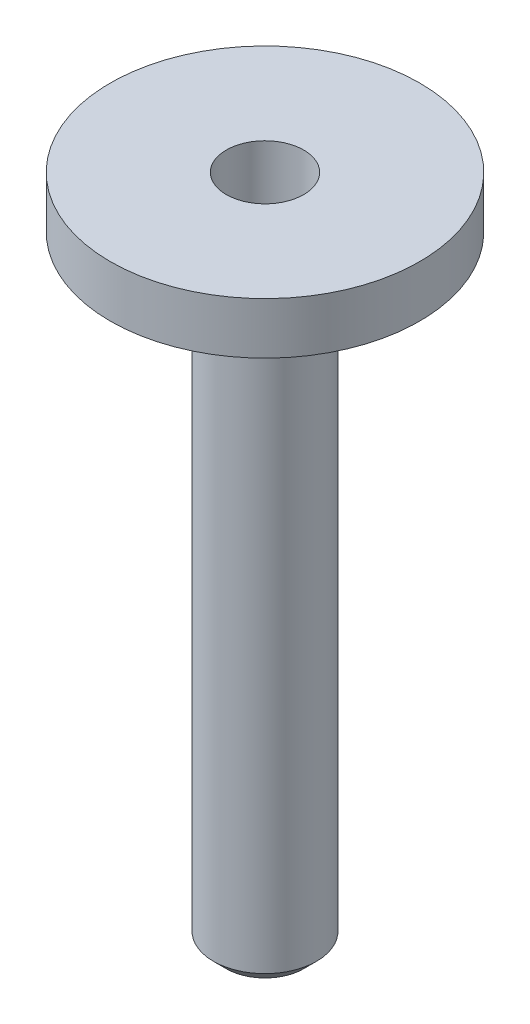
SolidWorks part; units mm, degrees
ref_plane "Front Plane" through (0, 0, 0) normal (0, 0, 1) x (1, 0, 0)
ref_plane "Top Plane" through (0, 0, 0) normal (0, 1, 0) x (1, 0, 0)
ref_plane "Right Plane" through (0, 0, 0) normal (1, 0, 0) x (0, 0, -1)
sketch "Sketch1" plane through (0, 0, 0) normal (0, 0, 1) x (1, 0, 0)
  line L0 (0, 0) -> (-19.05, 0)
  line L1 (-19.05, 0) -> (-19.05, -6.35)
  line L2 (-14.1605, -6.35) -> (-6.35, -6.35)
  line L3 (-6.35, -6.35) -> (-6.35, -82.55)
  line L4 (-6.35, -82.55) -> (0, -82.55)
  line L5 (0, -82.55) -> (0, 0)
  line L6 (-19.05, -6.35) -> (-17.4625, -6.35)
  line L7 (-17.4625, -6.35) -> (-17.4625, -3.81)
  line L8 (-17.4625, -3.81) -> (-14.1605, -3.81)
  line L9 (-14.1605, -3.81) -> (-14.1605, -6.35)
  dimension "D1" = 76.2
  dimension "D2" = 6.35
  dimension "D3" = 19.05
  dimension "D4" = 6.35
  dimension "D5" = 2.54
  dimension "D6" = 3.302
  dimension "D7" = 1.5875
revolve "Revolve1" add sketch "Sketch1" angle 360 about L5
hole_wizard "3/8 (0.375) Diameter Hole1" positions "Sketch2" profile "Sketch3" hole size "3/8" standard "ANSI Inch"
sketch "Sketch2" plane through (0, 0, 0) normal (0, 1, 0) x (1, 0, 0)
  point P0 (0, 0)
sketch "Sketch3" plane through (0, 0, 0) normal (1, 0, 0) x (0, 0, 1)
  line L0 (0, 0) -> (0, 80.6491)
  line L1 (0, 80.6491) -> (4.7625, 77.7875)
  line L2 (4.7625, 77.7875) -> (4.7625, 0)
  line L5 (4.7625, 0) -> (0, 0)
  line L10 (0, 80.6491) -> (-4.7625, 77.7875) construction
  line L11 (0, -6.35) -> (0, 107.95) construction
  dimension "Hole Dia." = 9.525
  dimension "Hole Depth" = 77.7875
  dimension "Drill Angle" = 118
chamfer "Chamfer1" distance 1.5875 angle 45 1 edges at (0, -82.55, -6.35)
